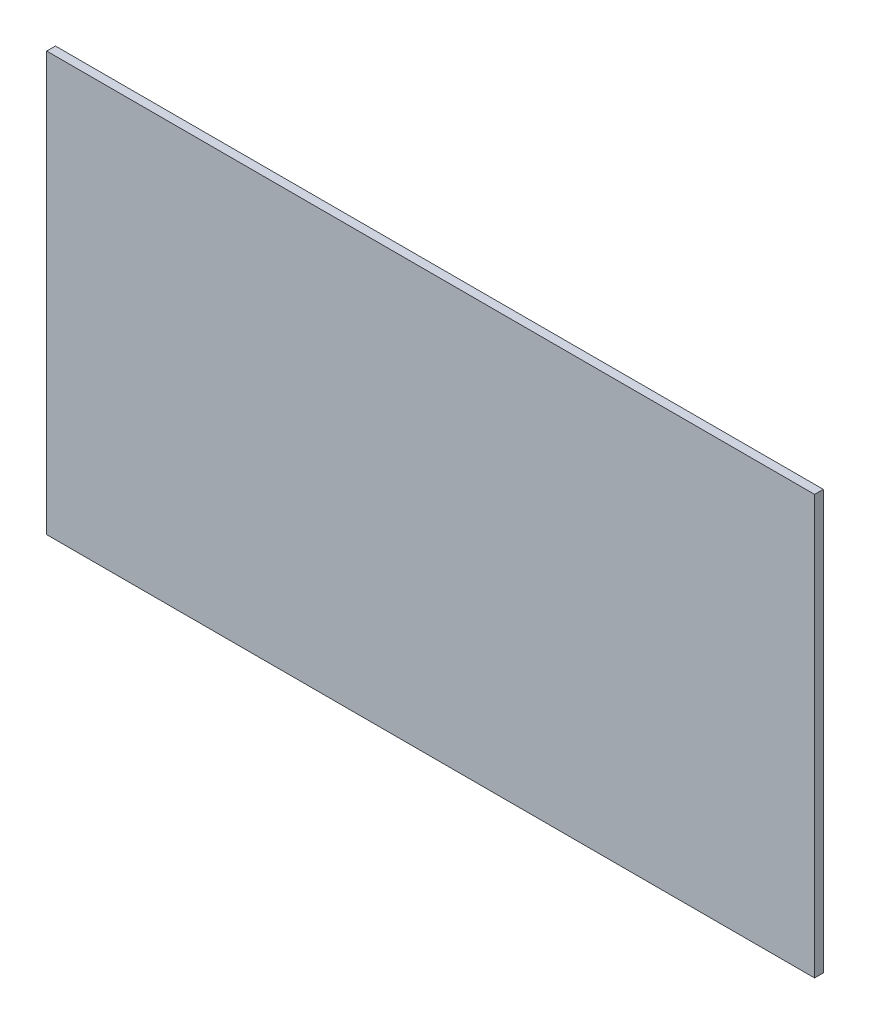
SolidWorks part; units mm, degrees
material "Glass"
ref_plane "Front Plane" through (0, 0, 0) normal (0, 0, 1) x (1, 0, 0)
ref_plane "Top Plane" through (0, 0, 0) normal (0, 1, 0) x (1, 0, 0)
ref_plane "Right Plane" through (0, 0, 0) normal (1, 0, 0) x (0, 0, -1)
sketch "Sketch1" plane through (0, 0, 0) normal (0, 0, 1) x (1, 0, 0)
  line L0 (440, -240) -> (440, 240) construction
  line L1 (440, 240) -> (-440, 240) construction
  line L2 (-440, 240) -> (-440, -240) construction
  line L3 (-440, -240) -> (440, -240) construction
  line L4 (440, -240) -> (440, 240)
  line L5 (440, 240) -> (-440, 240)
  line L6 (-440, 240) -> (-440, -240)
  line L7 (-440, -240) -> (440, -240)
extrude "Boss-Extrude1" add sketch "Sketch1" along normal blind 10
